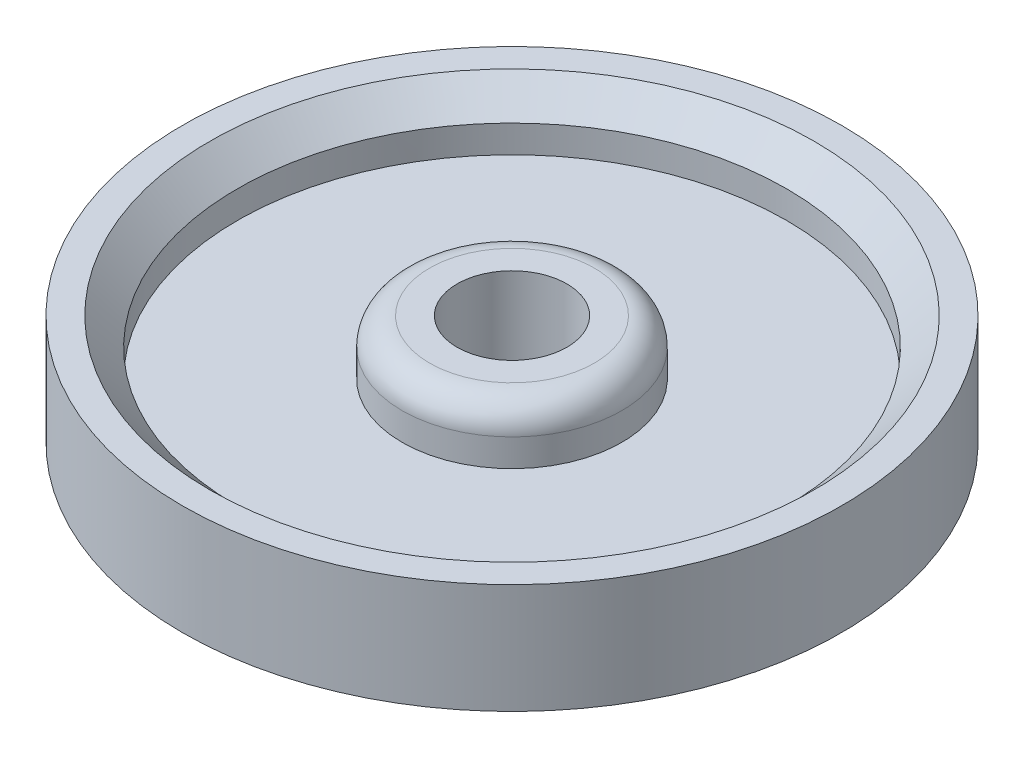
SolidWorks part; units mm, degrees
ref_plane "Plan de face" through (0, 0, 0) normal (0, 0, 1) x (1, 0, 0)
ref_plane "Plan de dessus" through (0, 0, 0) normal (0, 1, 0) x (1, 0, 0)
ref_plane "Plan de droite" through (0, 0, 0) normal (1, 0, 0) x (0, 0, -1)
sketch "Esquisse1" plane through (0, 0, 0) normal (0, 1, 0) x (1, 0, 0)
  circle A0 centre (24.3015, 9.852) radius 20
  circle A1 centre (24.3015, 9.852) radius 50
  circle A2 centre (24.3015, 9.852) radius 60
extrude "Boss.-Extru.1" add sketch "Esquisse1" along normal blind 20 contours A0 | A2 A1
sketch "Esquisse2" plane through (0, 0, 0) normal (0, -1, 0) x (1, 0, 0)
  circle A0 centre (24.3015, -9.852) radius 50 construction
  circle A1 centre (24.3015, -9.852) radius 20 construction
  circle A2 centre (24.3015, -9.852) radius 50
  circle A3 centre (24.3015, -9.852) radius 20
extrude "Boss.-Extru.2" add sketch "Esquisse2" against normal blind 10
chamfer "Chanfrein1" distance 5 angle 45 1 edges at (24.3015, 20, 40.148)
fillet "Congé1" radius 5 1 edges at (24.3015, 20, 10.148)
sketch "Esquisse3" plane through (0, 20, 0) normal (0, 1, 0) x (1, 0, 0)
  circle A0 centre (24.3015, 9.852) radius 10
extrude "Enlèv. mat.-Extru.1" cut sketch "Esquisse3" against normal blind 82
